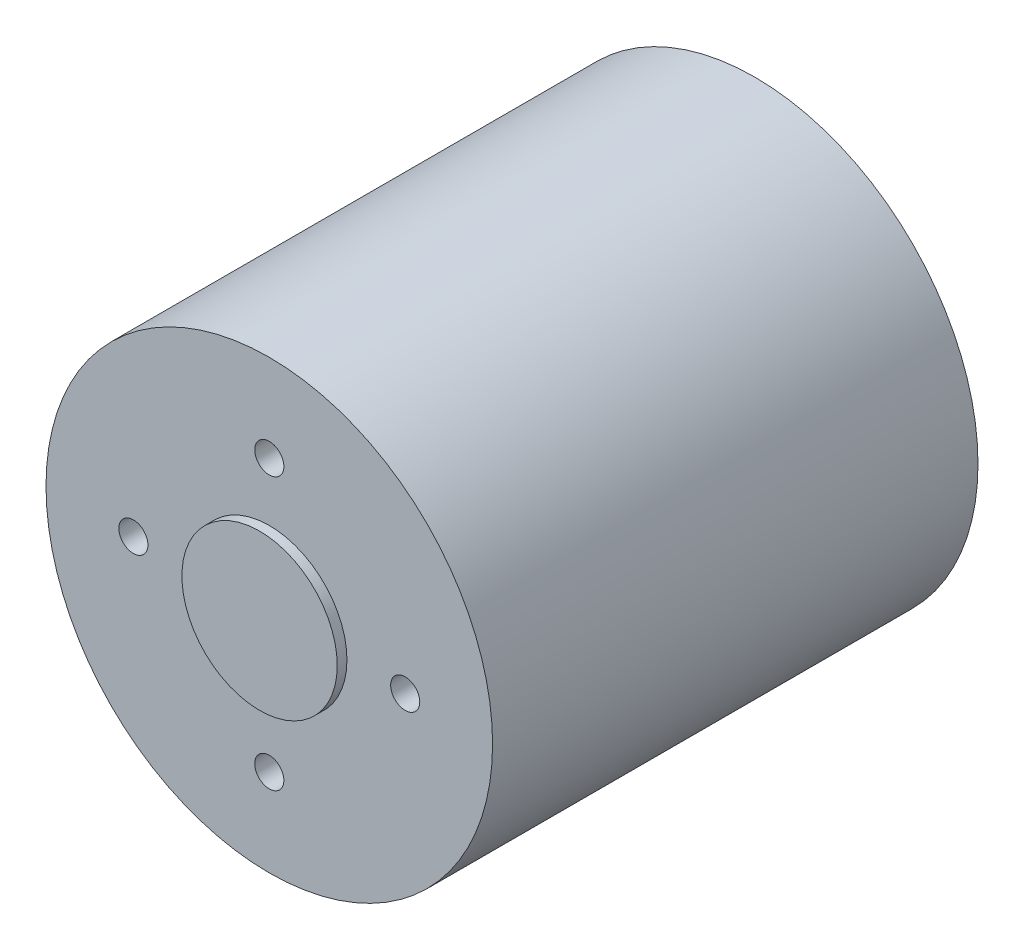
SolidWorks part; units mm, degrees
ref_plane "Front Plane" through (0, 0, 0) normal (0, 0, 1) x (1, 0, 0)
ref_plane "Top Plane" through (0, 0, 0) normal (0, 1, 0) x (1, 0, 0)
ref_plane "Right Plane" through (0, 0, 0) normal (1, 0, 0) x (0, 0, -1)
sketch "Sketch1" plane through (0, 0, 0) normal (0, 0, 1) x (1, 0, 0)
  circle A0 centre (0, 0) radius 23
  dimension "D1" = 46
extrude "Boss-Extrude1" add sketch "Sketch1" against normal blind 50
sketch "Sketch2" plane through (0, 0, 0) normal (0, 0, 1) x (1, 0, 0)
  circle A0 centre (0, 0) radius 8
  dimension "D1" = 16
extrude "Boss-Extrude2" add sketch "Sketch2" along normal blind 1
sketch "Sketch5" plane through (0, 0, -50) normal (0, 0, -1) x (-1, 0, 0)
  circle A0 centre (0, 0) radius 12.5 construction
  circle A1 centre (-12.5, 0) radius 1.5
  dimension "D1" = 25
  dimension "D2" = 3
extrude "Cut-Extrude2" cut sketch "Sketch5" against normal blind 10
sketch "Sketch6" plane through (0, 0, 0) normal (0, 0, 1) x (1, 0, 0)
  circle A0 centre (0, 0) radius 14 construction
  circle A1 centre (0, 14) radius 1.5
  dimension "D1" = 3
  dimension "D5" = 28
extrude "Cut-Extrude3" cut sketch "Sketch6" against normal blind 5
pattern_circular "CirPattern1" count 4 over 360 about axis through (0, 0, 0) along (0, 0, 1) of "Cut-Extrude3"
pattern_circular "CirPattern2" count 4 over 360 about axis through (0, 0, 0) along (0, 0, 1) of "Cut-Extrude2"
sketch "Sketch7" plane through (0, 0, -50) normal (0, 0, -1) x (-1, 0, 0)
  circle A0 centre (0, 0) radius 5
  dimension "D1" = 10
extrude "Boss-Extrude3" add sketch "Sketch7" along normal blind 5
sketch "Sketch8" plane through (0, 0, -55) normal (0, 0, -1) x (-1, 0, 0)
  circle A0 centre (0, 0) radius 2.425
  dimension "D1" = 4.85
extrude "Boss-Extrude4" add sketch "Sketch8" along normal blind 5
